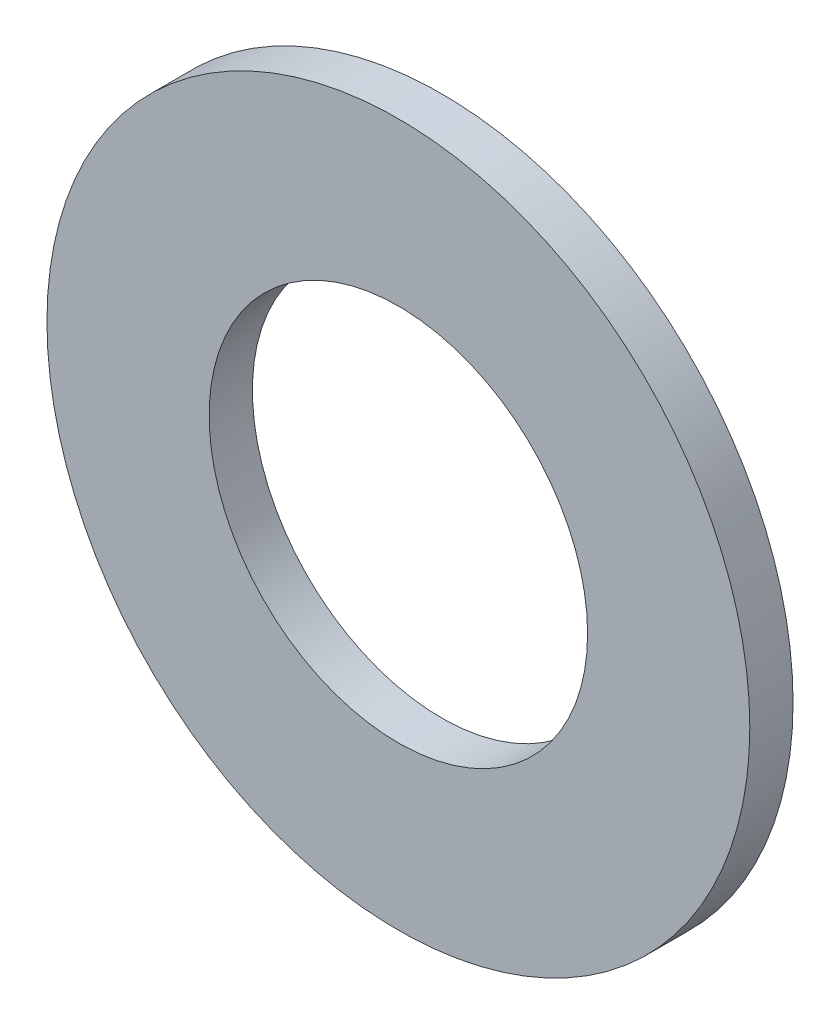
SolidWorks part; units mm, degrees
ref_plane "Front" through (0, 0, 0) normal (0, 0, 1) x (1, 0, 0)
ref_plane "Top" through (0, 0, 0) normal (0, 1, 0) x (1, 0, 0)
ref_plane "Right" through (0, 0, 0) normal (1, 0, 0) x (0, 0, -1)
sketch "Sketch1" plane through (0, 0, 0) normal (0, 0, 1) x (1, 0, 0)
  circle A0 centre (0, 0) radius 32.5
  circle A1 centre (0, 0) radius 17.5
  dimension "D1" = 65
  dimension "D2" = 35
extrude "Boss-Extrude1" add sketch "Sketch1" along normal blind 4
